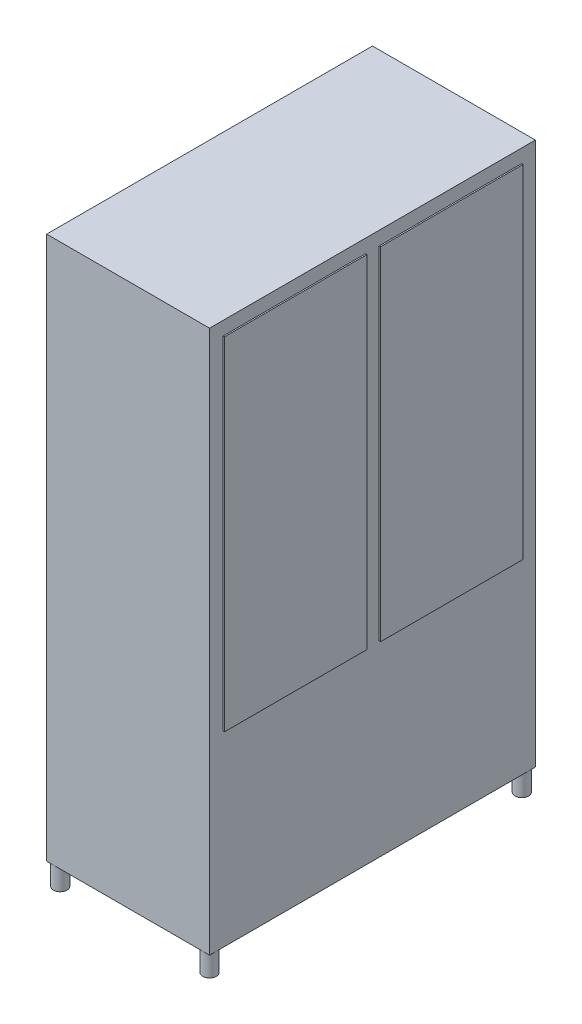
SolidWorks part; units mm, degrees
material "红木"
ref_plane "前视基准面" through (0, 0, 0) normal (0, 0, 1) x (1, 0, 0)
ref_plane "上视基准面" through (0, 0, 0) normal (0, 1, 0) x (1, 0, 0)
ref_plane "右视基准面" through (0, 0, 0) normal (1, 0, 0) x (0, 0, -1)
sketch "草图1" plane through (0, 0, 0) normal (0, 1, 0) x (1, 0, 0)
  line L1 (-300, -600) -> (300, -600)
  line L2 (-300, -600) -> (-300, 600)
  line L3 (-300, 600) -> (300, 600)
  line L4 (300, -600) -> (300, 600)
  line L5 (-300, -600) -> (300, 600) construction
  line L6 (-300, 600) -> (300, -600) construction
  point P0 (0, 0)
  dimension "D1" = 600
  dimension "D2" = 1200
extrude "凸台-拉伸1" add sketch "草图1" along normal blind 2000
sketch "草图2" plane through (0, 0, 0) normal (0, -1, 0) x (1, 0, 0)
  line L0 (300, 600) -> (300, -600) construction
  line L2 (-300, 600) -> (300, 600) construction
  circle A0 centre (275, 575) radius 25
  dimension "D1" = 50
extrude "凸台-拉伸2" add sketch "草图2" along normal blind 80
mirror "镜向1" about plane through (0, 0, 0) normal (1, 0, 0) of "凸台-拉伸2"
mirror "镜向2" about plane through (0, 0, 0) normal (0, 0, 1) of "镜向1", "凸台-拉伸2"
sketch "草图3" plane through (300, 0, 0) normal (1, 0, 0) x (0, 0, -1)
  line L0 (0, 2000) -> (0, 0) construction
  line L1 (-600, 2000) -> (600, 2000) construction
  line L2 (-600, 2000) -> (-600, 0) construction
  line L3 (-550, 1950) -> (-25, 1950)
  line L4 (-550, 1950) -> (-550, 690)
  line L5 (-550, 690) -> (-25, 690)
  line L6 (-25, 1950) -> (-25, 690)
  dimension "D1" = 50
  dimension "D2" = 50
  dimension "D3" = 50
  dimension "D4" = 1260
extrude "凸台-拉伸3" add sketch "草图3" along normal blind 5
mirror "镜向3" about plane through (0, 0, 0) normal (0, 0, 1) of "凸台-拉伸3"
